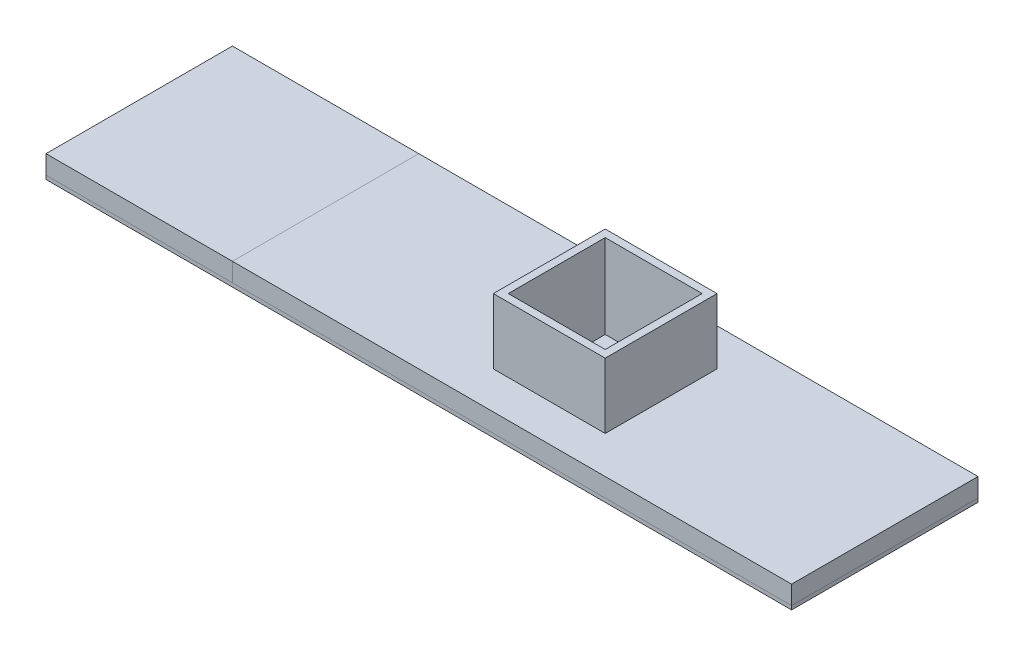
SolidWorks part; units mm, degrees
material "Silicon Dioxide"
ref_plane "Front Plane" through (0, 0, 0) normal (0, 0, 1) x (1, 0, 0)
ref_plane "Top Plane" through (0, 0, 0) normal (0, 1, 0) x (1, 0, 0)
ref_plane "Right Plane" through (0, 0, 0) normal (1, 0, 0) x (0, 0, -1)
sketch "Sketch1" plane through (0, 0, 0) normal (0, 1, 0) x (1, 0, 0)
  line L1 (-37.5, -12.5) -> (37.5, -12.5)
  line L2 (-37.5, -12.5) -> (-37.5, 12.5)
  line L3 (-37.5, 12.5) -> (37.5, 12.5)
  line L4 (37.5, -12.5) -> (37.5, 12.5)
  line L5 (-37.5, -12.5) -> (37.5, 12.5) construction
  line L6 (-37.5, 12.5) -> (37.5, -12.5) construction
  point P0 (0, 0)
  dimension "D1" = 25
  dimension "D2" = 75
extrude "Slide" add sketch "Sketch1" along normal mid plane 2.5
sketch "Sketch4" plane through (0, 0, 0) normal (0, 1, 0) x (1, 0, 0)
  line L1 (-37.5, 12.5) -> (-62.5, 12.5)
  line L2 (-37.5, 12.5) -> (-37.5, -12.5)
  line L3 (-37.5, -12.5) -> (-62.5, -12.5)
  line L4 (-62.5, 12.5) -> (-62.5, -12.5)
  dimension "D1" = 25
extrude "Label" add sketch "Sketch4" along normal mid plane 2.5 separate body
sketch "Sketch5" plane through (0, 0, 0) normal (0, 1, 0) x (1, 0, 0)
  line L1 (-6.5, -6.5) -> (6.5, -6.5)
  line L2 (-6.5, -6.5) -> (-6.5, 6.5)
  line L3 (-6.5, 6.5) -> (6.5, 6.5)
  line L4 (6.5, -6.5) -> (6.5, 6.5)
  line L5 (-6.5, -6.5) -> (6.5, 6.5) construction
  line L6 (-6.5, 6.5) -> (6.5, -6.5) construction
  line L7 (-7.5, -7.5) -> (7.5, -7.5)
  line L8 (-7.5, -7.5) -> (-7.5, 7.5)
  line L9 (-7.5, 7.5) -> (7.5, 7.5)
  line L10 (7.5, -7.5) -> (7.5, 7.5)
  line L11 (-7.5, -7.5) -> (7.5, 7.5) construction
  line L12 (-7.5, 7.5) -> (7.5, -7.5) construction
  point P0 (0, 0)
  point P6 (0, 0)
  dimension "D1" = 1
  dimension "D2" = 15
extrude "Boss-Extrude1" add sketch "Sketch5" along normal blind 10
sketch "Sketch6" plane through (0, 1.25, 0) normal (0, 1, 0) x (1, 0, 0)
  line L1 (-6.5, -6.5) -> (6.5, -6.5)
  line L2 (-6.5, -6.5) -> (-6.5, 6.5)
  line L3 (-6.5, 6.5) -> (6.5, 6.5)
  line L4 (6.5, -6.5) -> (6.5, 6.5)
  line L5 (-6.5, -6.5) -> (6.5, 6.5) construction
  line L6 (-6.5, 6.5) -> (6.5, -6.5) construction
  point P0 (0, 0)
extrude "Cut-Extrude1" cut sketch "Sketch6" against normal up to next (2.5 mm away)
sketch "Sketch7" plane through (-62.5, 0, 0) normal (-1, 0, 0) x (0, 0, 1)
  line L1 (-12.5, -1.25) -> (12.5, -1.25)
  line L2 (-12.5, -1.25) -> (-12.5, -1.75)
  line L3 (-12.5, -1.75) -> (12.5, -1.75)
  line L4 (12.5, -1.25) -> (12.5, -1.75)
  point P5 (0, 0)
  dimension "D1" = 0.5
extrude "Boss-Extrude2" add sketch "Sketch7" against normal up to surface (100 mm away) separate body up to face at (37.5, 0, 0)
